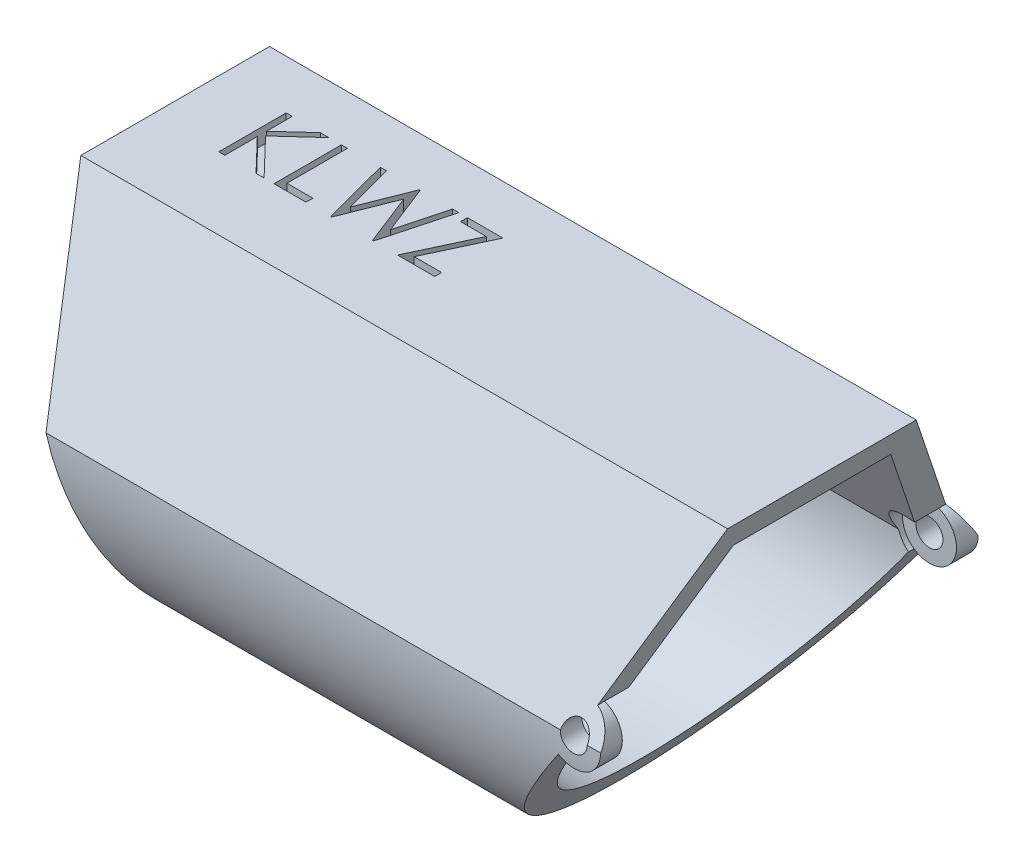
SolidWorks part; units mm, degrees
material "1060 Alloy"
ref_plane "Front Plane" through (0, 0, 0) normal (0, 0, 1) x (1, 0, 0)
ref_plane "Top Plane" through (0, 0, 0) normal (0, 1, 0) x (1, 0, 0)
ref_plane "Right Plane" through (0, 0, 0) normal (1, 0, 0) x (0, 0, -1)
sketch "Sketch1" plane through (0, 0, 0) normal (1, 0, 0) x (0, 0, -1)
  line L0 (-4.445, 0) -> (4.445, 0)
  line L1 (4.445, 0) -> (8.89, -7.699)
  line L2 (-4.445, 0) -> (-8.89, -7.699)
  arc A1 (-8.89, -7.699) -> (8.89, -7.699) centre (0, -8.207) ccw
  point P6 (0, 0)
  dimension "D1" = 120
  dimension "D3" = 17.78
  dimension "D2" = 120
  dimension "D4" = 0.508
extrude "Boss-Extrude1" add sketch "Sketch1" along normal blind 30.48
shell "Shell1" thickness 1.27
sketch "Sketch2" plane through (0, 0, 0) normal (0, 0, 1) x (1, 0, 0)
  line L0 (30.48, 0) -> (28.1122, -6.5056)
  line L1 (30.48, -7.699) -> (0, -7.699) construction
  line L3 (0, -17.1115) -> (30.48, -17.1115) construction
  line L4 (30.48, 0) -> (0, 0) construction
  line L5 (30.48, 0) -> (30.48, -17.1115)
  line L6 (30.48, -17.1115) -> (21.0871, -17.1115)
  line L7 (0, 0) -> (6.2281, -17.1115)
  line L8 (0, -17.1115) -> (6.2281, -17.1115)
  line L9 (0, 0) -> (0, -17.1115)
  line L12 (0, 0) -> (0, -7.699) construction
  line L13 (0, -17.1115) -> (30.48, -17.1115) construction
  line L15 (26.9494, -8.7393) -> (21.0871, -17.1115)
  arc A0 (28.1122, -6.5056) -> (26.9494, -8.7393) centre (27.6778, -7.699) cw
  circle A1 centre (27.6778, -7.699) radius 0.635
  dimension "D4" = 1.27
  dimension "D5" = 1.27
  dimension "D1" = 70
  dimension "D3" = 70
extrude "Cut-Extrude1" cut sketch "Sketch2" against normal through all both and the other way through all
sketch "Sketch4" plane through (0, 0, 0) normal (0, 0, 1) x (1, 0, 0)
  circle A0 centre (27.6778, -7.699) radius 1.27
extrude "Cut-Extrude3" cut sketch "Sketch4" against normal blind 7.874 and the other way blind 7.874
ref_plane "Plane1" through (0, -17.1115, 0) normal (0, 1, 0) x (1, 0, 0)
sketch "Sketch5" plane through (0, -17.1115, 0) normal (0, 1, 0) x (1, 0, 0)
  line L1 (5.4661, 1.27) -> (6.9901, 1.27)
  line L2 (5.4661, 1.27) -> (5.4661, -1.27)
  line L3 (5.4661, -1.27) -> (6.9901, -1.27)
  line L4 (6.9901, 1.27) -> (6.9901, -1.27)
  line L5 (5.4661, 1.27) -> (6.9901, -1.27) construction
  line L6 (5.4661, -1.27) -> (6.9901, 1.27) construction
  ellipse E0 centre (2.9871, 0) end of major axis (2.9871, -8.9045) minor radius 3.241 (2.8022, -8.89) -> (2.8022, 8.89) ccw construction
  point P0 (6.2281, 0)
  point P12 (0, 0)
  dimension "D1" = 1.524
  dimension "D2" = 2.54
extrude "Cut-Extrude5" cut sketch "Sketch5" along normal blind 0.508
sketch "Sketch3" plane through (0, 0, 0) normal (0, 1, 0) x (1, 0, 0)
  text T0 "KLWZ" font "Century Gothic" height in points 12
extrude "Cut-Extrude2" cut sketch "Sketch3" against normal blind 0.762
